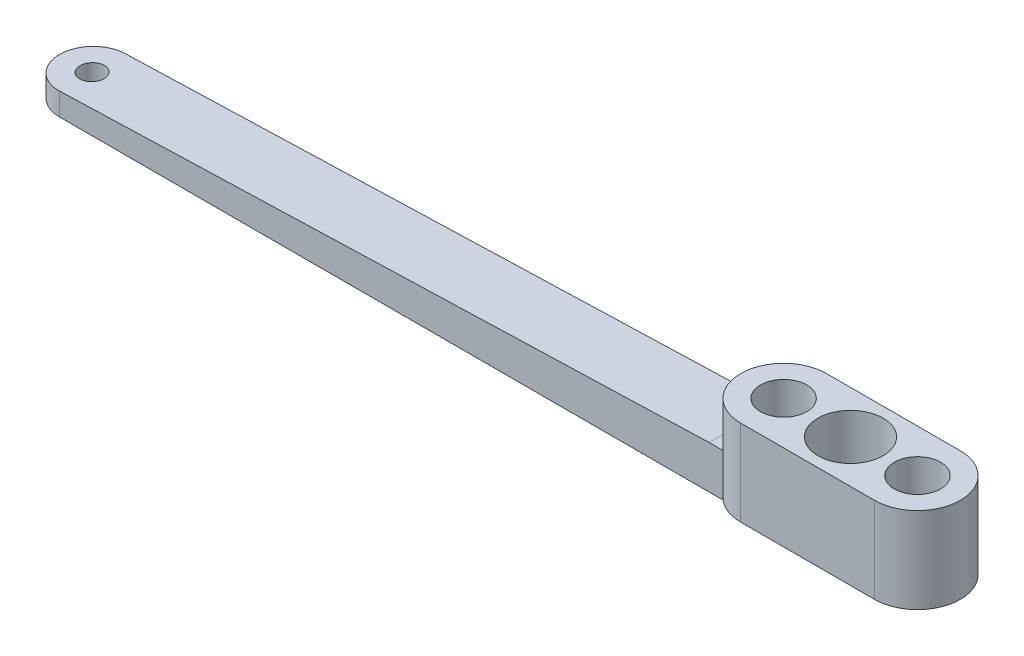
SolidWorks part; units mm, degrees
ref_plane "Front Plane" through (0, 0, 0) normal (0, 0, 1) x (1, 0, 0)
ref_plane "Top Plane" through (0, 0, 0) normal (0, 1, 0) x (1, 0, 0)
ref_plane "Right Plane" through (0, 0, 0) normal (1, 0, 0) x (0, 0, -1)
sketch "Sketch1" plane through (0, 0, 0) normal (0, 1, 0) x (1, 0, 0)
  line L0 (-9.906, 0) -> (9.906, 0) construction
  line L1 (-9.906, 6.35) -> (9.906, 6.35)
  line L2 (-9.906, -6.35) -> (9.906, -6.35)
  arc A0 (-9.906, 6.35) -> (-9.906, -6.35) centre (-9.906, 0) ccw
  arc A1 (9.906, -6.35) -> (9.906, 6.35) centre (9.906, 0) ccw
  circle A2 centre (0, 0) radius 4.826
  circle A3 centre (9.906, 0) radius 3.429
  circle A4 centre (-9.906, 0) radius 3.429
  point P3 (0, 0)
  dimension "D1" = 6.858
  dimension "D3" = 9.652
  dimension "D4" = 6.858
  dimension "D2" = 9.906
  dimension "D5" = 12.7
extrude "Boss-Extrude1" add sketch "Sketch1" along normal blind 12.7
sketch "Sketch2" plane through (0, 0, 0) normal (0, 1, 0) x (1, 0, 0)
  circle A0 centre (-9.906, 0) radius 3.429
  circle A1 centre (-9.906, 0) radius 1.905
  circle A2 centre (9.906, 0) radius 3.429
  circle A3 centre (9.906, 0) radius 1.905
  dimension "D1" = 3.81
  dimension "D2" = 3.81
  dimension "D3" = 6.858
  dimension "D4" = 6.858
extrude "Boss-Extrude2" add sketch "Sketch2" along normal blind 6.35
sketch "Sketch4" plane through (0, 0, 0) normal (0, 1, 0) x (1, 0, 0)
  line L0 (0, 0) -> (-112.268, 0)
  line L1 (-112.268, -4.826) -> (-14.033, -4.826)
  line L2 (-112.268, -4.826) -> (-112.268, 0)
  line L3 (-112.268, 4.826) -> (-14.033, 4.826)
  arc A0 (-112.268, 4.826) -> (-112.268, -4.826) centre (-112.268, 0) ccw
  arc A1 (-9.906, 6.35) -> (-9.906, -6.35) centre (-9.906, 0) ccw construction
  arc A2 (-14.033, 4.826) -> (-14.033, -4.826) centre (-9.906, 0) ccw
  dimension "D3" = 4.826
  dimension "D1" = 112.268
  dimension "D2" = 4.826
  dimension "D4" = 98.235
extrude "Boss-Extrude4" add sketch "Sketch4" along normal blind 6.35 contours A2 L0 L2 L1 | A2 L3 A0 L2 L0
sketch "Sketch5" plane through (0, 0, 0) normal (0, 0, 1) x (1, 0, 0)
  line L0 (-117.094, 0) -> (-117.094, 3.175)
  line L1 (-117.094, 6.35) -> (-117.094, 0) construction
  line L2 (-117.094, 3.175) -> (-16.1104, 6.35)
  line L3 (-112.268, 6.35) -> (-14.033, 6.35) construction
  line L4 (-16.1104, 6.35) -> (-16.1104, 3.175)
  line L5 (-16.1104, 3.175) -> (-117.094, 3.175)
  line L6 (-117.094, 3.175) -> (-117.094, 6.35)
  line L7 (-117.094, 6.35) -> (-16.1104, 6.35)
  dimension "D1" = 100.9836
extrude "Cut-Extrude1" cut sketch "Sketch5" against normal through all both and the other way through all contours L7 L6 L2
sketch "Sketch6" plane through (0, 0, 0) normal (0, 1, 0) x (1, 0, 0)
  line L0 (-16.1104, -4.826) -> (-112.268, -4.826) construction
  circle A0 centre (-112.268, 0) radius 1.778
  dimension "D1" = 3.556
  dimension "D2" = 4.826
extrude "Cut-Extrude2" cut sketch "Sketch6" along normal blind 6.35
